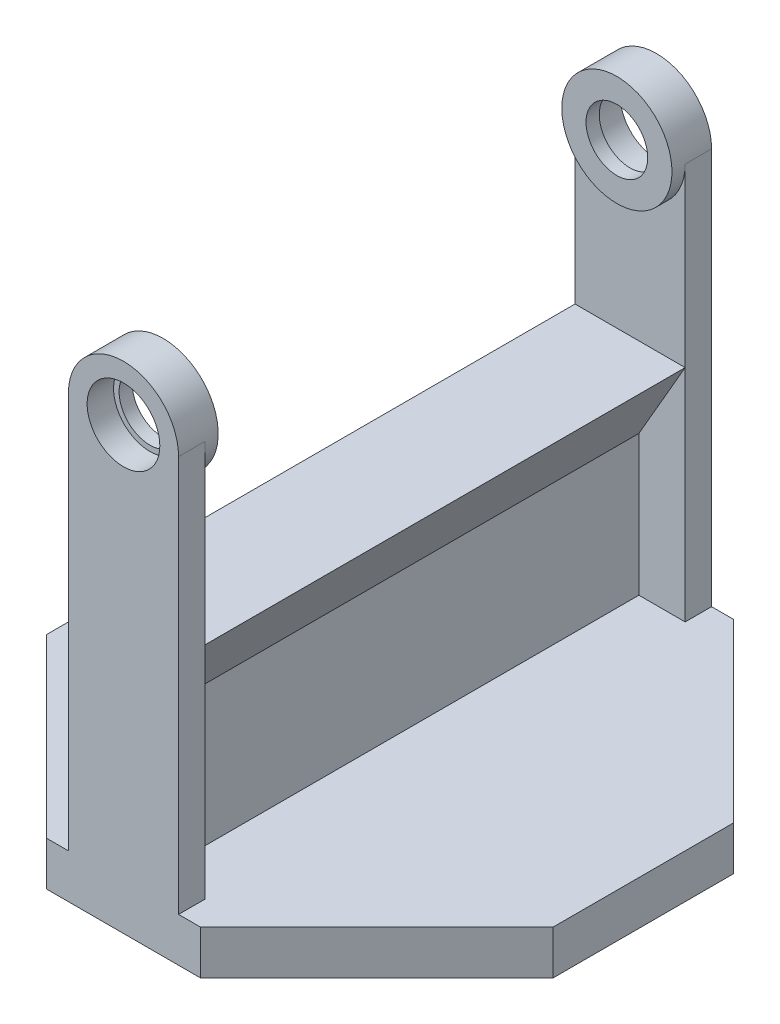
SolidWorks part; units mm, degrees
ref_plane "Front" through (0, 0, 0) normal (0, 0, 1) x (1, 0, 0)
ref_plane "Top" through (0, 0, 0) normal (0, 1, 0) x (1, 0, 0)
ref_plane "Right" through (0, 0, 0) normal (1, 0, 0) x (0, 0, -1)
sketch "Sketch1" plane through (0, 0, 0) normal (0, 1, 0) x (1, 0, 0)
  line L1 (-57.5, -60.5) -> (57.5, -60.5)
  line L2 (-57.5, -60.5) -> (-57.5, 60.5)
  line L3 (-57.5, 60.5) -> (57.5, 60.5)
  line L4 (57.5, -60.5) -> (57.5, 60.5)
  line L5 (-57.5, -60.5) -> (57.5, 60.5) construction
  line L6 (-57.5, 60.5) -> (57.5, -60.5) construction
  point P0 (0, 0)
  dimension "D1" = 121
  dimension "D2" = 115
extrude "Boss-Extrude1" add sketch "Sketch1" along normal blind 10
sketch "Sketch2" plane through (0, 0, 60.5) normal (0, 0, 1) x (1, 0, 0)
  line L0 (-12.5, 100) -> (-12.5, 0)
  line L2 (-12.5, 0) -> (12.5, 0)
  line L3 (12.5, 100) -> (12.5, 0)
  line L4 (-12.5, 100) -> (12.5, 0) construction
  line L5 (-12.5, 0) -> (12.5, 100) construction
  arc A0 (12.5, 100) -> (-12.5, 100) centre (0, 100) ccw
  point P0 (0, 0)
  point P1 (0, 50)
  dimension "D1" = 25
  dimension "D2" = 100
extrude "Boss-Extrude2" add sketch "Sketch2" against normal blind 6
sketch "Sketch3" plane through (0, 0, 54.5) normal (0, 0, -1) x (-1, 0, 0)
  circle A0 centre (0, 100) radius 12.5
  circle A1 centre (0, 100) radius 7
  dimension "D1" = 14
extrude "Boss-Extrude3" add sketch "Sketch3" along normal blind 3
sketch "Sketch4" plane through (0, 0, 60.5) normal (0, 0, 1) x (1, 0, 0)
  circle A0 centre (0, 100) radius 8.25
  dimension "D1" = 16.5
extrude "Cut-Extrude1" cut sketch "Sketch4" against normal up to surface (6 mm away) up to face at (0, 51.875, 54.5)
sketch "Sketch6" plane through (0, 0, 0) normal (1, 0, 0) x (0, 0, -1)
  line L0 (-54.5, 10) -> (-54.5, 60)
  line L1 (-54.5, 10) -> (-54.5, 100) construction
  line L3 (-60.5, 10) -> (60.5, 10) construction
  line L4 (0, 10) -> (-54.5, 10)
  line L5 (0, 10) -> (0, 60)
  line L6 (0, 60) -> (-54.5, 60)
  dimension "D1" = 50
  dimension "D2" = 50
extrude "Boss-Extrude5" add sketch "Sketch6" along normal blind 2 and the other way blind 2
mirror "Mirror1" about plane through (0, 0, 0) normal (0, 0, 1) of "Boss-Extrude5", "Cut-Extrude1", "Boss-Extrude3", "Boss-Extrude2"
sketch "Sketch7" plane through (0, 0, -54.5) normal (0, 0, 1) x (1, 0, 0)
  line L0 (0, 0) -> (0, -50000) construction
  line L1 (-57.5, 0) -> (57.5, 0) construction
  line L2 (2, 60) -> (12.5, 60)
  line L3 (12.5, 10) -> (12.5, 100) construction
  line L4 (12.5, 60) -> (2, 41.8135)
  line L5 (2, 60) -> (2, 10) construction
  line L6 (2, 60) -> (2, 41.8135)
  line L7 (-2, 60) -> (-12.5, 60)
  line L8 (-12.5, 60) -> (-2, 41.8135)
  line L9 (-2, 60) -> (-2, 41.8135)
  point P4 (0, 0)
  dimension "D1" = 30
extrude "Boss-Extrude6" add sketch "Sketch7" along normal up to next
chamfer "Chamfer1" distance 40 angle 45 4 edges at (57.5, 5, -60.5) (57.5, 5, 60.5) (-57.5, 5, -60.5) (-57.5, 5, 60.5)
